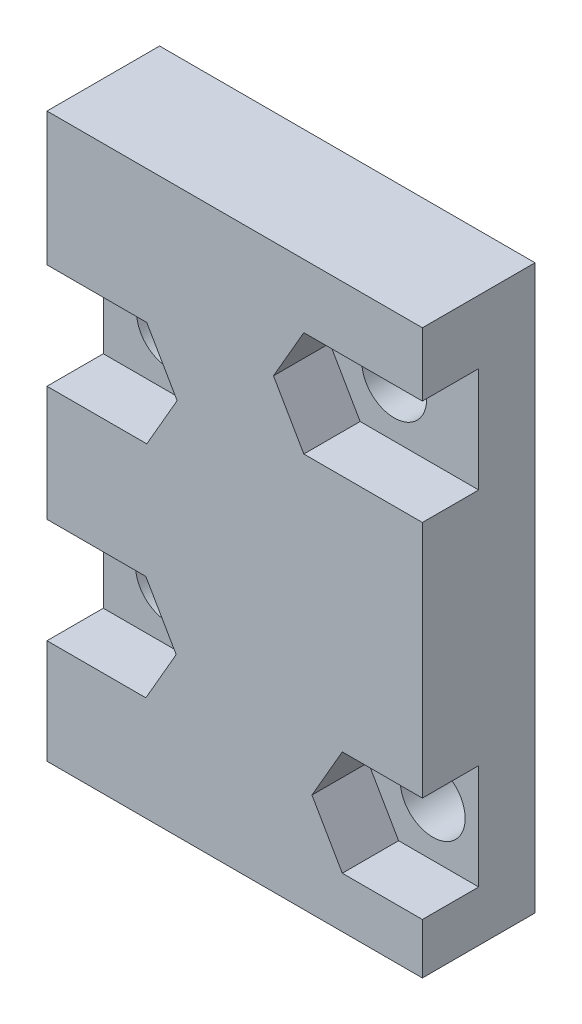
SolidWorks part; units mm, degrees
ref_plane "Front Plane" through (0, 0, 0) normal (0, 0, 1) x (1, 0, 0)
ref_plane "Top Plane" through (0, 0, 0) normal (0, 1, 0) x (1, 0, 0)
ref_plane "Right Plane" through (0, 0, 0) normal (1, 0, 0) x (0, 0, -1)
sketch "Sketch1" plane through (0, 0, 0) normal (0, 0, 1) x (1, 0, 0)
  line L1 (0, 0) -> (20, 0)
  line L2 (0, 0) -> (0, 30)
  line L3 (0, 30) -> (20, 30)
  line L4 (20, 0) -> (20, 30)
  dimension "D1" = 30
  dimension "D2" = 20
extrude "Boss-Extrude1" add sketch "Sketch1" along normal blind 6
sketch "Sketch2" plane through (0, 0, 6) normal (0, 0, 1) x (1, 0, 0)
  line L0 (20, 0) -> (20, 30) construction
  line L1 (0, 30) -> (0, 0) construction
  line L2 (0, 0) -> (20, 0) construction
  circle A0 centre (15.5, 23.8167) radius 1.7279
  circle A1 centre (3.5, 20.1026) radius 1.7279
  circle A2 centre (17.55, 5.5) radius 1.7279
  circle A3 centre (3.45, 8.3612) radius 1.7279
  dimension "D1" = 4.5
  dimension "D2" = 3.5
  dimension "D3" = 2.45
  dimension "D4" = 3.45
  dimension "D5" = 5.5
extrude "Cut-Extrude1" cut sketch "Sketch2" against normal through all
sketch "Sketch3" plane through (0, 0, 6) normal (0, 0, 1) x (1, 0, 0)
  line L0 (15.3, 23.8167) -> (15.5, 23.8167) construction
  line L1 (17.6691, 22.3201) -> (18.5332, 23.8167) construction
  line L2 (18.5332, 23.8167) -> (16.3302, 27.6323) construction
  line L3 (20, 26.6167) -> (13.6834, 26.6167)
  line L4 (13.6834, 26.6167) -> (12.0668, 23.8167)
  line L5 (12.0668, 23.8167) -> (13.6834, 21.0167)
  line L6 (13.6834, 21.0167) -> (20, 21.0167)
  line L7 (20, 26.6167) -> (20, 21.0167)
  line L8 (20, 0) -> (20, 30) construction
  line L9 (3.45, 8.3612) -> (3.65, 8.3612) construction
  line L10 (6.9332, 20.1026) -> (5.3166, 22.9026)
  line L11 (5.3166, 22.9026) -> (0, 22.9026)
  line L12 (2.0834, 22.9026) -> (0.4668, 20.1026) construction
  line L13 (0.4668, 20.1026) -> (2.0834, 17.3026) construction
  line L14 (0, 17.3026) -> (5.3166, 17.3026)
  line L15 (5.3166, 17.3026) -> (6.9332, 20.1026)
  line L16 (6.8832, 8.3612) -> (5.2666, 11.1612)
  line L17 (5.2666, 11.1612) -> (0, 11.1612)
  line L18 (2.0334, 11.1612) -> (0.4168, 8.3612) construction
  line L19 (0.4168, 8.3612) -> (2.0334, 5.5612) construction
  line L20 (0, 5.5612) -> (5.2666, 5.5612)
  line L21 (5.2666, 5.5612) -> (6.8832, 8.3612)
  line L22 (14.1168, 5.5) -> (15.7334, 2.7)
  line L23 (15.7334, 2.7) -> (20, 2.7)
  line L24 (18.8261, 2.4567) -> (20.5832, 5.5) construction
  line L25 (20.5832, 5.5) -> (19.1071, 8.0567) construction
  line L26 (20, 8.3) -> (15.7334, 8.3)
  line L27 (15.7334, 8.3) -> (14.1168, 5.5)
  line L28 (17.55, 5.5) -> (17.35, 5.5) construction
  line L29 (3.5, 20.1026) -> (3.7, 20.1026) construction
  line L30 (20, 2.7) -> (20, 8.3)
  line L31 (0, 5.5612) -> (0, 11.1612)
  line L32 (0, 30) -> (0, 0) construction
  line L33 (0, 17.3026) -> (0, 22.9026)
  circle A0 centre (15.3, 23.8167) radius 2.8 construction
  circle A1 centre (3.7, 20.1026) radius 2.8 construction
  circle A2 centre (3.65, 8.3612) radius 2.8 construction
  circle A3 centre (17.35, 5.5) radius 2.8 construction
  dimension "D1" = 5.6
  dimension "D2" = 0.2
extrude "Cut-Extrude2" cut sketch "Sketch3" against normal blind 3
